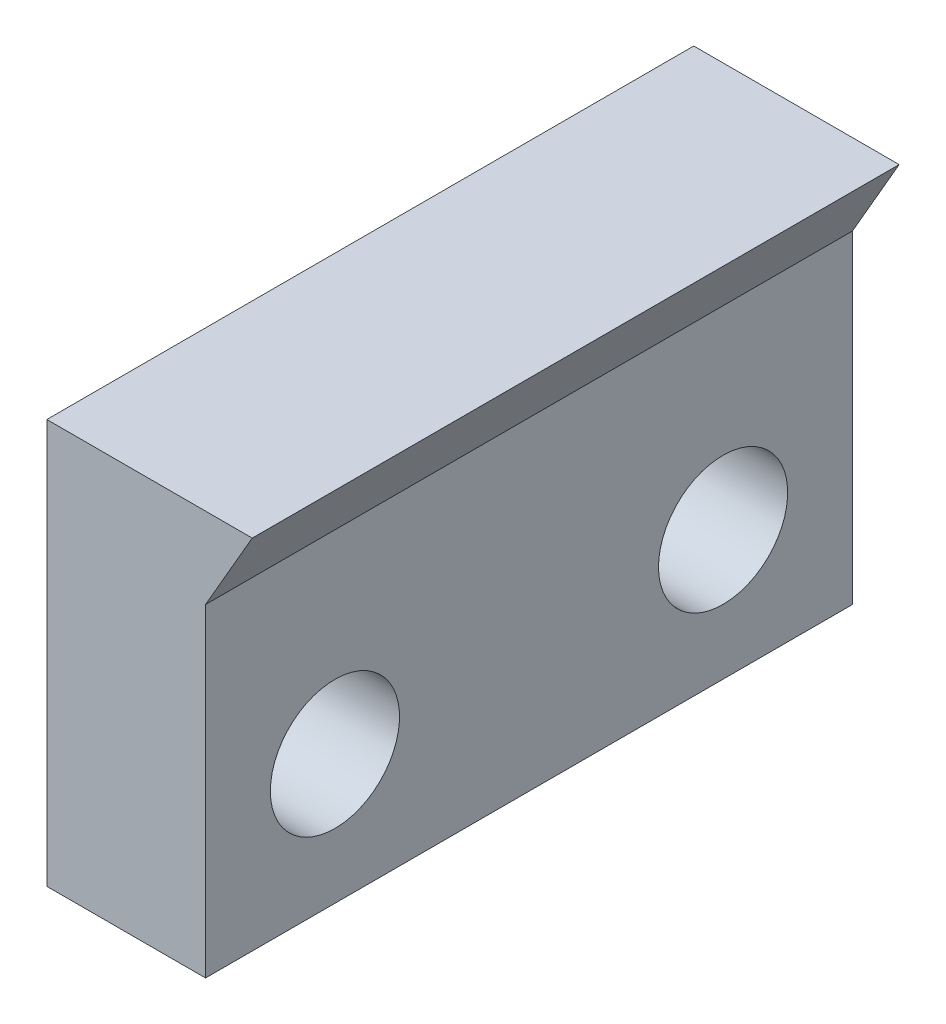
SolidWorks part; units mm, degrees
ref_plane "Front Plane" through (0, 0, 0) normal (0, 0, 1) x (1, 0, 0)
ref_plane "Top Plane" through (0, 0, 0) normal (0, 1, 0) x (1, 0, 0)
ref_plane "Right Plane" through (0, 0, 0) normal (1, 0, 0) x (0, 0, -1)
sketch "Sketch2" plane through (0, 0, 0) normal (0, 0, 1) x (1, 0, 0)
  line L1 (0, 0) -> (-9.8132, 0)
  line L2 (0, 0) -> (0, 20)
  line L4 (-9.8132, 0) -> (-9.8132, 25)
  line L5 (2.8868, 25) -> (0, 20)
  line L6 (-9.8132, 25) -> (2.8868, 25)
  dimension "D1" = 12.7
  dimension "D2" = 30
  dimension "D3" = 20
  dimension "D4" = 5
sketch "Sketch3" plane through (0, 0, 0) normal (0, 0, 1) x (1, 0, 0)
  line L1 (-9.8132, 0) -> (0, 0)
  line L2 (-9.8132, 0) -> (-9.8132, -2)
  line L3 (-9.8132, -2) -> (0, -2)
  line L4 (0, 0) -> (0, -2)
  dimension "D1" = 2
extrude "Boss-Extrude1" add sketch "Sketch2" along normal mid plane 40
sketch "Sketch4" plane through (-9.8132, 0, 0) normal (-1, 0, 0) x (0, 0, 1)
  line L0 (20, 0) -> (-20, 0) construction
  circle A0 centre (-12, 8) radius 3.9942
  dimension "D2" = 7.9883
  dimension "D1" = 12
  dimension "D3" = 8
extrude "Cut-Extrude1" cut sketch "Sketch4" against normal through all
mirror "Mirror1" about plane through (0, 0, 0) normal (0, 0, 1) of "Cut-Extrude1"
equation "\"H\" = 12"
equation "\"D1@Sketch4\"=\"H\""
equation "\"D\" = 6.604"
